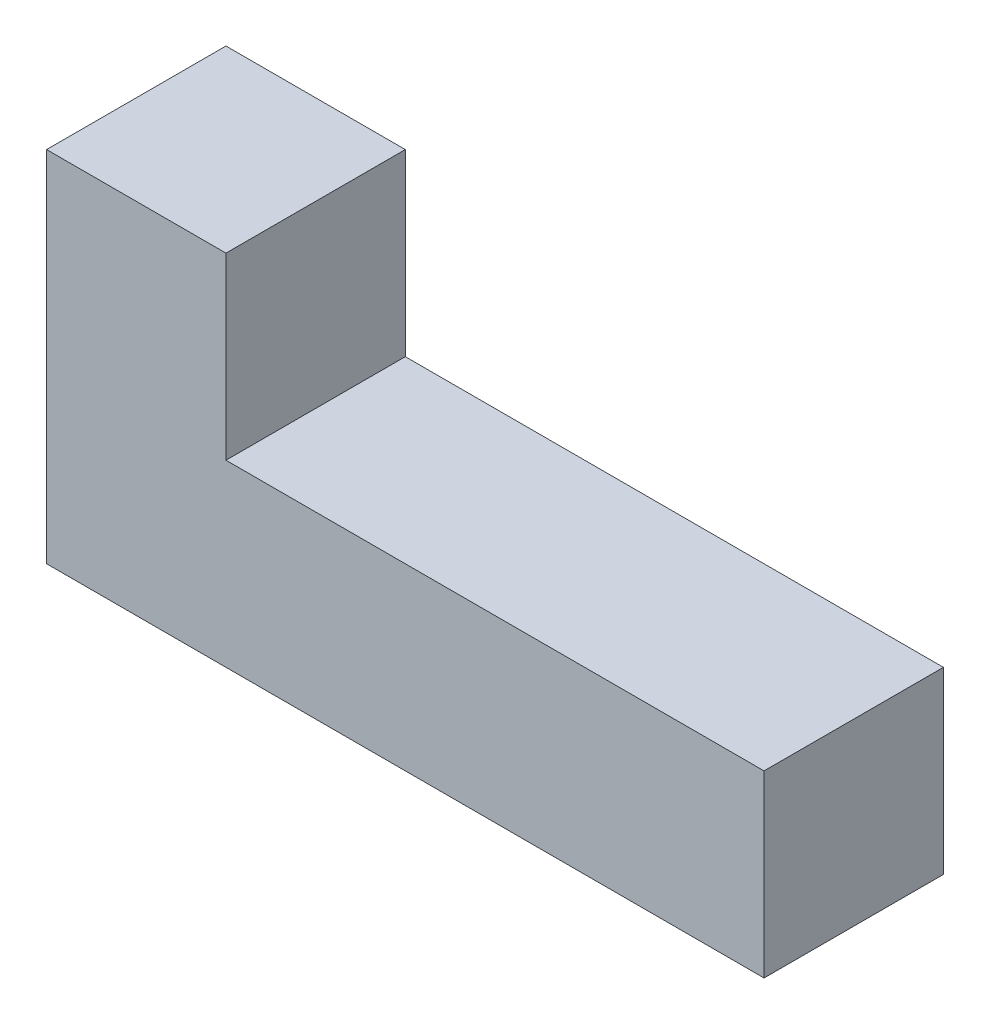
SolidWorks part; units mm, degrees
ref_plane "Front Plane" through (0, 0, 0) normal (0, 0, 1) x (1, 0, 0)
ref_plane "Top Plane" through (0, 0, 0) normal (0, 1, 0) x (1, 0, 0)
ref_plane "Right Plane" through (0, 0, 0) normal (1, 0, 0) x (0, 0, -1)
sketch "Sketch1" plane through (0, 0, 0) normal (0, 0, 1) x (1, 0, 0)
  line L8 (101.6, 0) -> (101.6, 25.4)
  line L9 (101.6, 25.4) -> (25.4, 25.4)
  line L10 (25.4, 25.4) -> (25.4, 50.8)
  line L11 (25.4, 50.8) -> (0, 50.8)
  line L12 (0, 50.8) -> (0, 0)
  line L13 (0, 0) -> (101.6, 0)
extrude "Boss-Extrude1" add sketch "Sketch1" along normal blind 25.4
